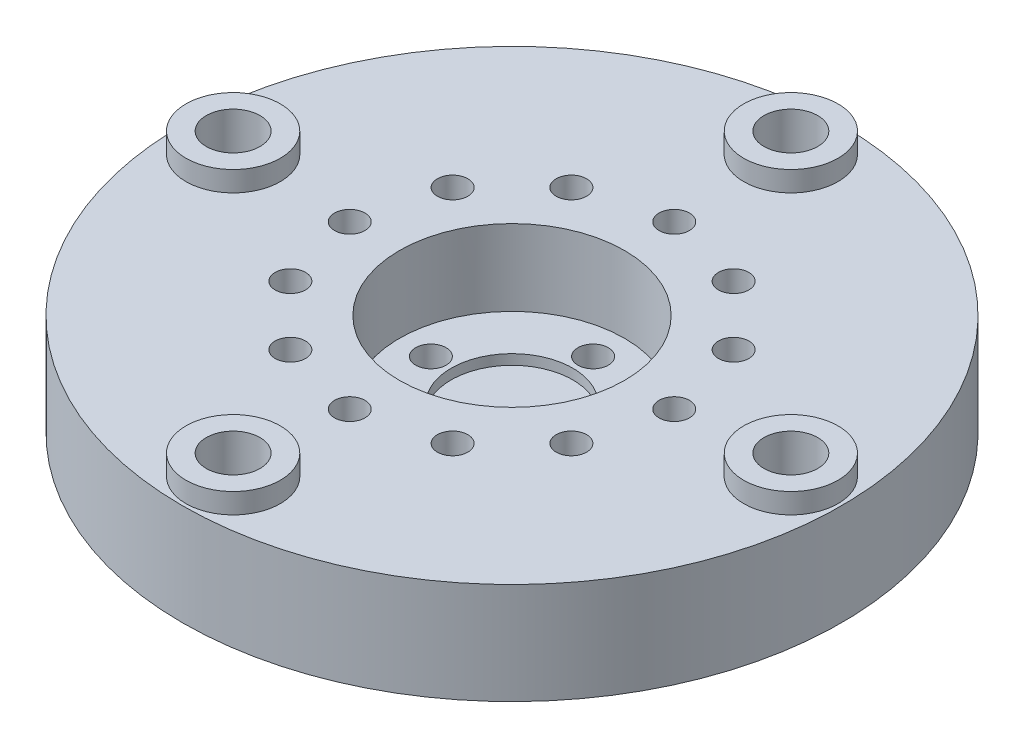
SolidWorks part; units mm, degrees
ref_plane "Front Plane" through (0, 0, 0) normal (0, 0, 1) x (1, 0, 0)
ref_plane "Top Plane" through (0, 0, 0) normal (0, 1, 0) x (1, 0, 0)
ref_plane "Right Plane" through (0, 0, 0) normal (1, 0, 0) x (0, 0, -1)
sketch "Sketch1" plane through (0, 0, 0) normal (0, 1, 0) x (1, 0, 0)
  circle A0 centre (0, 0) radius 32.5
  circle A1 centre (0, 27.5) radius 2.65
  circle A2 centre (27.5, 0) radius 2.65
  circle A3 centre (0, -27.5) radius 2.65
  circle A4 centre (-27.5, 0) radius 2.65
  circle A5 centre (0, 0) radius 11.1
  point P14 (0, 0)
  dimension "D1" = 65
  dimension "D2" = 5.3
  dimension "D5" = 22.2
  dimension "D3" = 27.5
  dimension "D4" = 4
extrude "Boss-Extrude1" add sketch "Sketch1" along normal blind 3
sketch "Sketch2" plane through (0, 3, 0) normal (0, 1, 0) x (1, 0, 0)
  circle A0 centre (0, -27.5) radius 2.65 construction
  circle A1 centre (27.5, 0) radius 2.65 construction
  circle A2 centre (0, 27.5) radius 2.65 construction
  circle A3 centre (-27.5, 0) radius 2.65 construction
  circle A4 centre (0, -27.5) radius 2.65
  circle A5 centre (27.5, 0) radius 2.65
  circle A6 centre (0, 27.5) radius 2.65
  circle A7 centre (-27.5, 0) radius 2.65
  circle A8 centre (0, -27.5) radius 4.65
  circle A9 centre (27.5, 0) radius 4.65
  circle A10 centre (0, 27.5) radius 4.65
  circle A11 centre (-27.5, 0) radius 4.65
  dimension "D1" = 2
extrude "Boss-Extrude2" add sketch "Sketch2" along normal blind 2
sketch "Sketch3" plane through (0, 0, 0) normal (0, -1, 0) x (-1, 0, 0)
  circle A0 centre (0, 0) radius 11.1 construction
  circle A1 centre (0, 0) radius 32.5 construction
  circle A2 centre (0, 0) radius 11.1
  circle A3 centre (0, 0) radius 32.5
  circle A4 centre (0, 27.5) radius 4.25
  circle A5 centre (27.5, 0) radius 4.25
  circle A6 centre (0, -27.5) radius 4.25
  circle A7 centre (-27.5, 0) radius 4.25
  point P18 (0, 0)
  dimension "D1" = 8.5
  dimension "D2" = 4
extrude "Boss-Extrude3" add sketch "Sketch3" along normal blind 7
sketch "Sketch4" plane through (0, -7, 0) normal (0, -1, 0) x (-1, 0, 0)
  circle A0 centre (0, 0) radius 11.1 construction
  circle A1 centre (0, 0) radius 11.1
  circle A2 centre (0, 8) radius 1.5
  circle A3 centre (8, 0) radius 1.5
  circle A4 centre (0, -8) radius 1.5
  circle A5 centre (-8, 0) radius 1.5
  point P14 (0, 0)
  dimension "D2" = 3
  dimension "D1" = 8
  dimension "D3" = 4
extrude "Boss-Extrude4" add sketch "Sketch4" against normal blind 2.5
sketch "Sketch5" plane through (0, -7, 0) normal (0, -1, 0) x (1, 0, 0)
  circle A0 centre (0, 16) radius 1.5
  circle A1 centre (8, 13.8564) radius 1.5
  circle A2 centre (13.8564, 8) radius 1.5
  circle A3 centre (16, 0) radius 1.5
  circle A4 centre (13.8564, -8) radius 1.5
  circle A5 centre (8, -13.8564) radius 1.5
  circle A6 centre (0, -16) radius 1.5
  circle A7 centre (-8, -13.8564) radius 1.5
  circle A8 centre (-13.8564, -8) radius 1.5
  circle A9 centre (-16, 0) radius 1.5
  circle A10 centre (-13.8564, 8) radius 1.5
  circle A11 centre (-8, 13.8564) radius 1.5
  point P27 (0, 0)
  dimension "D2" = 3
  dimension "D1" = 16
  dimension "D3" = 12
extrude "Cut-Extrude1" cut sketch "Sketch5" against normal through all
sketch "Sketch6" plane through (0, -4.5, 0) normal (0, 1, 0) x (1, 0, 0)
  circle A0 centre (0, 0) radius 6
  dimension "D1" = 12
extrude "Cut-Extrude2" cut sketch "Sketch6" against normal blind 1
